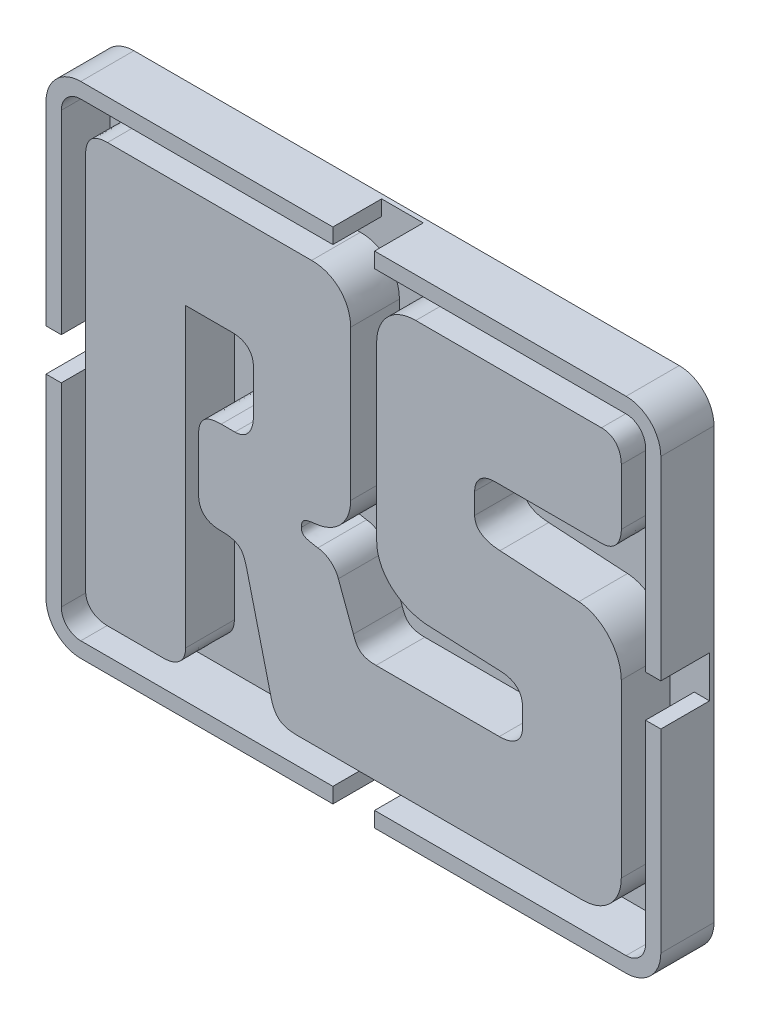
SolidWorks part; units mm, degrees
ref_plane "Front Plane" through (0, 0, 0) normal (0, 0, 1) x (1, 0, 0)
ref_plane "Top Plane" through (0, 0, 0) normal (0, 1, 0) x (1, 0, 0)
ref_plane "Right Plane" through (0, 0, 0) normal (1, 0, 0) x (0, 0, -1)
sketch "Sketch1" plane through (0, 0, 0) normal (0, 0, 1) x (1, 0, 0)
  line L0 (40.5984, 31.4849) -> (40.5984, 17.9224)
  line L1 (40.5984, 17.9224) -> (41.6324, 17.9224)
  line L2 (41.6324, 17.9224) -> (41.6324, 31.4849)
  line L3 (39.2783, 33.8385) -> (21.8474, 33.8385)
  line L4 (21.8474, 33.8385) -> (21.8474, 32.8044)
  line L5 (21.8474, 32.8044) -> (39.2783, 32.8044)
  line L6 (1.0341, 2.3536) -> (1.0341, 15.9005)
  line L7 (1.0341, 15.9005) -> (0, 15.9005)
  line L8 (0, 15.9005) -> (0, 2.3536)
  line L9 (2.3549, 0) -> (19.8255, 0)
  line L10 (19.8255, 0) -> (19.8255, 1.0341)
  line L11 (19.8255, 1.0341) -> (2.3549, 1.0341)
  line L12 (0, 31.4849) -> (0, 17.9225)
  line L13 (0, 17.9225) -> (1.0341, 17.9225)
  line L14 (1.0341, 17.9225) -> (1.0341, 31.4849)
  line L15 (2.3549, 32.8045) -> (19.8256, 32.8045)
  line L16 (19.8256, 32.8045) -> (19.8256, 33.8385)
  line L17 (19.8256, 33.8385) -> (2.3549, 33.8385)
  line L18 (40.5984, 15.9006) -> (40.5984, 2.3536)
  line L19 (39.2783, 1.0341) -> (21.8474, 1.0341)
  line L20 (21.8474, 1.0341) -> (21.8474, 0.0001)
  line L21 (21.8474, 0.0001) -> (39.2788, 0.0001)
  line L22 (41.6324, 2.3542) -> (41.6324, 15.9006)
  line L23 (41.6324, 15.9006) -> (40.5984, 15.9006)
  line L24 (30.4178, 24.3897) -> (37.612, 24.3844)
  line L25 (37.6119, 31.1578) -> (25.0374, 31.1624)
  line L26 (25.7334, 13.6975) -> (30.7888, 13.4646)
  line L27 (32.2731, 12.0731) -> (32.2718, 10.8666)
  line L28 (30.6966, 9.5909) -> (22.3472, 9.5909)
  line L29 (20.8154, 10.6573) -> (19.7956, 13.3946)
  line L30 (20.6305, 18.4034) -> (20.6305, 28.5623)
  line L31 (17.9866, 31.1605) -> (4.1631, 31.1605)
  line L32 (2.6794, 29.6753) -> (2.6794, 4.1632)
  line L33 (9.4513, 4.1632) -> (9.4513, 24.2491)
  line L34 (9.4513, 24.2491) -> (12.6055, 24.2491)
  line L35 (14.0435, 22.9496) -> (14.0435, 20.0279)
  line L36 (12.7913, 18.4963) -> (11.8629, 18.4963)
  line L37 (10.3333, 17.1511) -> (10.3333, 13.5799)
  line L38 (13.5804, 10.9359) -> (15.25, 4.1175)
  line L39 (17.1054, 2.8175) -> (36.3092, 2.8181)
  line L40 (38.9536, 5.4147) -> (38.9536, 17.0373)
  line L41 (36.0776, 20.1908) -> (30.7423, 20.5153)
  line L42 (29.0263, 21.7218) -> (29.0263, 23.1376)
  spline S0 degree 3 poles (41.6324, 31.4849) (41.6324, 32.7827) (40.5763, 33.8385) (39.2783, 33.8385) knots 0 0 0 0 1 1 1 1
  spline S1 degree 3 poles (39.2783, 32.8044) (40.0061, 32.8044) (40.5984, 32.2125) (40.5984, 31.4849) knots 0 0 0 0 1 1 1 1
  spline S2 degree 3 poles (0, 2.3536) (0, 1.0558) (1.0564, 0) (2.3549, 0) knots 0 0 0 0 1 1 1 1
  spline S3 degree 3 poles (2.3549, 1.0341) (1.6266, 1.0341) (1.0341, 1.626) (1.0341, 2.3536) knots 0 0 0 0 1 1 1 1
  spline S4 degree 3 poles (2.3549, 33.8385) (1.0564, 33.8385) (0, 32.7827) (0, 31.4849) knots 0 0 0 0 1 1 1 1
  spline S5 degree 3 poles (1.0341, 31.4849) (1.0341, 32.2125) (1.6266, 32.8045) (2.3549, 32.8045) knots 0 0 0 0 1 1 1 1
  spline S6 degree 3 poles (40.5984, 2.3536) (40.5984, 1.6261) (40.0061, 1.0341) (39.2783, 1.0341) knots 0 0 0 0 1 1 1 1
  spline S7 degree 3 poles (39.2788, 0.0001) (40.5769, 0.0004) (41.6327, 1.0564) (41.6324, 2.3542) knots 0 0 0 0 1 1 1 1
  spline S8 degree 3 poles (37.612, 24.3844) (38.6319, 24.3844) (38.9565, 25.2192) (38.9565, 25.8695) knots 0 0 0 0 1 1 1 1
  spline S9 degree 3 poles (38.9565, 25.8695) (38.9565, 26.0419) (38.9571, 29.26) (38.9571, 29.6726) knots 0 0 0 0 1 1 1 1
  spline S10 degree 3 poles (38.9571, 29.6726) (38.9571, 30.323) (38.6319, 31.1578) (37.6119, 31.1578) knots 0 0 0 0 1 1 1 1
  spline S11 degree 3 poles (25.0374, 31.1624) (23.367, 31.1624) (22.393, 29.9102) (22.393, 28.5651) knots 0 0 0 0 1 1 1 1
  spline S12 degree 3 poles (22.393, 28.5651) (22.393, 27.875) (22.3936, 17.6103) (22.3936, 16.8974) knots 0 0 0 0 1 1 1 1
  spline S13 degree 3 poles (22.3936, 16.8974) (22.3936, 15.1813) (23.878, 13.882) (25.7334, 13.6975) knots 0 0 0 0 1 1 1 1
  spline S14 degree 3 poles (30.7888, 13.4646) (31.9028, 13.4188) (32.2731, 12.8156) (32.2731, 12.0731) knots 0 0 0 0 1 1 1 1
  spline S15 degree 3 poles (32.2718, 10.8666) (32.2423, 10.073) (31.6889, 9.5909) (30.6966, 9.5909) knots 0 0 0 0 1 1 1 1
  spline S16 degree 3 poles (22.3472, 9.5909) (21.1878, 9.5909) (21.002, 10.1468) (20.8154, 10.6573) knots 0 0 0 0 1 1 1 1
  spline S17 degree 3 poles (19.7956, 13.3946) (19.6104, 13.9507) (19.0537, 14.4618) (18.404, 14.5075) knots 0 0 0 0 1 1 1 1
  spline S18 degree 3 poles (18.404, 14.5075) (17.5235, 14.6461) (17.2912, 14.7389) (17.2912, 15.1563) knots 0 0 0 0 1 1 1 1
  spline S19 degree 3 poles (17.2912, 15.1563) (17.2912, 15.7139) (17.5692, 15.7604) (18.3111, 15.8524) knots 0 0 0 0 1 1 1 1
  spline S20 degree 3 poles (18.3111, 15.8524) (19.6104, 15.9919) (20.6305, 17.0119) (20.6305, 18.4034) knots 0 0 0 0 1 1 1 1
  spline S21 degree 3 poles (20.6305, 28.5623) (20.6305, 29.9081) (19.6568, 31.1605) (17.9866, 31.1605) knots 0 0 0 0 1 1 1 1
  spline S22 degree 3 poles (4.1631, 31.1605) (3.1426, 31.1605) (2.6794, 30.6501) (2.6794, 29.6753) knots 0 0 0 0 1 1 1 1
  spline S23 degree 3 poles (2.6794, 4.1632) (2.6794, 3.1427) (3.5135, 2.8181) (4.1631, 2.8181) knots 0 0 0 0 1 1 1 1
  spline S24 degree 3 poles (4.1631, 2.8181) (4.3355, 2.8181) (7.5542, 2.8175) (7.9669, 2.8175) knots 0 0 0 0 1 1 1 1
  spline S25 degree 3 poles (7.9669, 2.8175) (8.6167, 2.8175) (9.4513, 3.1427) (9.4513, 4.1632) knots 0 0 0 0 1 1 1 1
  spline S26 degree 3 poles (12.6055, 24.2491) (13.4874, 24.2491) (14.0435, 23.7853) (14.0435, 22.9496) knots 0 0 0 0 1 1 1 1
  spline S27 degree 3 poles (14.0435, 20.0279) (14.0435, 19.2383) (13.674, 18.4963) (12.7913, 18.4963) knots 0 0 0 0 1 1 1 1
  spline S28 degree 3 poles (11.8629, 18.4963) (10.7971, 18.4963) (10.3333, 18.0788) (10.3333, 17.1511) knots 0 0 0 0 1 1 1 1
  spline S29 degree 3 poles (10.3333, 13.5799) (10.3333, 12.6521) (10.9358, 12.2345) (11.7706, 12.2345) knots 0 0 0 0 1 1 1 1
  spline S30 degree 3 poles (11.7706, 12.2345) (13.1623, 12.2345) (13.3487, 11.7707) (13.5804, 10.9359) knots 0 0 0 0 1 1 1 1
  spline S31 degree 3 poles (15.25, 4.1175) (15.5286, 3.0033) (16.1311, 2.8175) (17.1054, 2.8175) knots 0 0 0 0 1 1 1 1
  spline S32 degree 3 poles (36.3092, 2.8181) (37.9795, 2.8181) (38.9536, 4.0711) (38.9536, 5.4147) knots 0 0 0 0 1 1 1 1
  spline S33 degree 3 poles (38.9536, 17.0373) (38.9536, 18.5677) (37.7014, 20.0979) (36.0776, 20.1908) knots 0 0 0 0 1 1 1 1
  spline S34 degree 3 poles (30.7423, 20.5153) (29.6294, 20.5617) (29.0263, 21.0256) (29.0263, 21.7218) knots 0 0 0 0 1 1 1 1
  spline S35 degree 3 poles (29.0263, 23.1376) (29.0263, 23.7871) (29.4444, 24.3897) (30.4178, 24.3897) knots 0 0 0 0 1 1 1 1
sketch "Sketch2" plane through (0, 0, 0) normal (0, 0, 1) x (1, 0, 0)
  line L2 (2.3536, 0.0001) -> (39.2788, 0.0001)
  line L3 (0, 2.3537) -> (0, 31.4849)
  line L4 (2.3549, 33.8385) -> (39.2788, 33.8385)
  line L6 (41.6324, 2.3537) -> (41.6324, 31.4849)
  arc A0 (39.2788, 33.8385) -> (41.6324, 31.4849) centre (39.2788, 31.4849) cw
  arc A1 (41.6324, 2.3537) -> (39.2788, 0.0001) centre (39.2788, 2.3537) cw
  arc A2 (2.3536, 0.0001) -> (0, 2.3537) centre (2.3536, 2.3537) cw
  arc A3 (0, 31.4849) -> (2.3549, 33.8385) centre (2.3536, 31.4849) cw
extrude "Boss-Extrude1" add sketch "Sketch2" along normal blind 3.6
sketch "Sketch6" plane through (0, 0, 3.6) normal (0, 0, 1) x (1, 0, 0)
  line L0 (40.5984, 31.4849) -> (40.5984, 18.3225)
  line L1 (40.5984, 18.3225) -> (42.9082, 18.3225)
  line L2 (-0.414, 18.3225) -> (-0.414, 15.5005)
  line L3 (19.4255, 34.3512) -> (22.2474, 34.3512)
  line L4 (22.2474, 34.3512) -> (22.2474, 32.8044)
  line L5 (22.2474, 32.8044) -> (39.2783, 32.8044)
  line L6 (1.0341, 2.3555) -> (1.0341, 15.5005)
  line L7 (1.0341, 15.5005) -> (-0.414, 15.5005)
  line L8 (0, 17.9225) -> (1.0341, 17.9225) construction
  line L9 (42.9082, 15.5005) -> (42.9082, 18.3225)
  line L10 (19.4255, -1.1352) -> (19.4255, 1.036)
  line L11 (19.4255, 1.036) -> (2.3549, 1.036)
  line L12 (22.2474, -1.1352) -> (19.4255, -1.1352)
  line L13 (-0.414, 18.3225) -> (1.0341, 18.3225)
  line L14 (1.0341, 18.3225) -> (1.0341, 31.4849)
  line L15 (2.3549, 32.8045) -> (19.4255, 32.8045)
  line L16 (19.4255, 32.8045) -> (19.4255, 34.3512)
  line L17 (1.0341, 15.9005) -> (0, 15.9005) construction
  line L18 (40.5984, 15.5005) -> (40.5984, 2.3555)
  line L19 (39.2783, 1.036) -> (22.2474, 1.036)
  line L20 (22.2474, 1.036) -> (22.2474, -1.1352)
  line L21 (19.8255, 0) -> (19.8255, 1.0341) construction
  line L22 (21.8474, 1.0341) -> (21.8474, 0.0001) construction
  line L23 (42.9082, 15.5005) -> (40.5984, 15.5005)
  line L24 (30.4178, 24.3897) -> (37.612, 24.3844)
  line L25 (37.6119, 31.1578) -> (25.0374, 31.1624)
  line L26 (25.7334, 13.6975) -> (30.7888, 13.4646)
  line L27 (32.2731, 12.0731) -> (32.2718, 10.8666)
  line L28 (30.6966, 9.5909) -> (22.3472, 9.5909)
  line L29 (20.8154, 10.6573) -> (19.7956, 13.3946)
  line L30 (20.6305, 18.4034) -> (20.6305, 28.5623)
  line L31 (17.9866, 31.1605) -> (4.1631, 31.1605)
  line L32 (2.6794, 29.6753) -> (2.6794, 4.1632)
  line L33 (9.4513, 4.1632) -> (9.4513, 24.2491)
  line L34 (9.4513, 24.2491) -> (12.6055, 24.2491)
  line L35 (14.0435, 22.9496) -> (14.0435, 20.0279)
  line L36 (12.7913, 18.4963) -> (11.8629, 18.4963)
  line L37 (10.3333, 17.1511) -> (10.3333, 13.5799)
  line L38 (13.5804, 10.9359) -> (15.25, 4.1175)
  line L39 (17.1054, 2.8175) -> (36.3092, 2.8181)
  line L40 (38.9536, 5.4147) -> (38.9536, 17.0373)
  line L41 (36.0776, 20.1908) -> (30.7423, 20.5153)
  line L42 (29.0263, 21.7218) -> (29.0263, 23.1376)
  line L43 (40.5984, 15.9006) -> (40.5984, 2.3536) construction
  line L44 (2.3549, 32.8045) -> (19.8256, 32.8045) construction
  spline S1 degree 3 poles (39.2783, 32.8044) (40.0061, 32.8044) (40.5984, 32.2125) (40.5984, 31.4849) knots 0 0 0 0 1 1 1 1
  spline S3 degree 3 poles (2.3549, 1.036) (1.6266, 1.036) (1.0341, 1.6279) (1.0341, 2.3555) knots 0 0 0 0 1 1 1 1
  spline S5 degree 3 poles (1.0341, 31.4849) (1.0341, 32.2125) (1.6266, 32.8045) (2.3549, 32.8045) knots 0 0 0 0 1 1 1 1
  spline S6 degree 3 poles (40.5984, 2.3555) (40.5984, 1.6279) (40.0061, 1.036) (39.2783, 1.036) knots 0 0 0 0 1 1 1 1
  spline S8 degree 3 poles (37.612, 24.3844) (38.6319, 24.3844) (38.9565, 25.2192) (38.9565, 25.8695) knots 0 0 0 0 1 1 1 1
  spline S9 degree 3 poles (38.9565, 25.8695) (38.9565, 26.0419) (38.9571, 29.26) (38.9571, 29.6726) knots 0 0 0 0 1 1 1 1
  spline S10 degree 3 poles (38.9571, 29.6726) (38.9571, 30.323) (38.6319, 31.1578) (37.6119, 31.1578) knots 0 0 0 0 1 1 1 1
  spline S11 degree 3 poles (25.0374, 31.1624) (23.367, 31.1624) (22.393, 29.9102) (22.393, 28.5651) knots 0 0 0 0 1 1 1 1
  spline S12 degree 3 poles (22.393, 28.5651) (22.393, 27.875) (22.3936, 17.6103) (22.3936, 16.8974) knots 0 0 0 0 1 1 1 1
  spline S13 degree 3 poles (22.3936, 16.8974) (22.3936, 15.1813) (23.878, 13.882) (25.7334, 13.6975) knots 0 0 0 0 1 1 1 1
  spline S14 degree 3 poles (30.7888, 13.4646) (31.9028, 13.4188) (32.2731, 12.8156) (32.2731, 12.0731) knots 0 0 0 0 1 1 1 1
  spline S15 degree 3 poles (32.2718, 10.8666) (32.2423, 10.073) (31.6889, 9.5909) (30.6966, 9.5909) knots 0 0 0 0 1 1 1 1
  spline S16 degree 3 poles (22.3472, 9.5909) (21.1878, 9.5909) (21.002, 10.1468) (20.8154, 10.6573) knots 0 0 0 0 1 1 1 1
  spline S17 degree 3 poles (19.7956, 13.3946) (19.6104, 13.9507) (19.0537, 14.4618) (18.404, 14.5075) knots 0 0 0 0 1 1 1 1
  spline S18 degree 3 poles (18.404, 14.5075) (17.5235, 14.6461) (17.2912, 14.7389) (17.2912, 15.1563) knots 0 0 0 0 1 1 1 1
  spline S19 degree 3 poles (17.2912, 15.1563) (17.2912, 15.7139) (17.5692, 15.7604) (18.3111, 15.8524) knots 0 0 0 0 1 1 1 1
  spline S20 degree 3 poles (18.3111, 15.8524) (19.6104, 15.9919) (20.6305, 17.0119) (20.6305, 18.4034) knots 0 0 0 0 1 1 1 1
  spline S21 degree 3 poles (20.6305, 28.5623) (20.6305, 29.9081) (19.6568, 31.1605) (17.9866, 31.1605) knots 0 0 0 0 1 1 1 1
  spline S22 degree 3 poles (4.1631, 31.1605) (3.1426, 31.1605) (2.6794, 30.6501) (2.6794, 29.6753) knots 0 0 0 0 1 1 1 1
  spline S23 degree 3 poles (2.6794, 4.1632) (2.6794, 3.1427) (3.5135, 2.8181) (4.1631, 2.8181) knots 0 0 0 0 1 1 1 1
  spline S24 degree 3 poles (4.1631, 2.8181) (4.3355, 2.8181) (7.5542, 2.8175) (7.9669, 2.8175) knots 0 0 0 0 1 1 1 1
  spline S25 degree 3 poles (7.9669, 2.8175) (8.6167, 2.8175) (9.4513, 3.1427) (9.4513, 4.1632) knots 0 0 0 0 1 1 1 1
  spline S26 degree 3 poles (12.6055, 24.2491) (13.4874, 24.2491) (14.0435, 23.7853) (14.0435, 22.9496) knots 0 0 0 0 1 1 1 1
  spline S27 degree 3 poles (14.0435, 20.0279) (14.0435, 19.2383) (13.674, 18.4963) (12.7913, 18.4963) knots 0 0 0 0 1 1 1 1
  spline S28 degree 3 poles (11.8629, 18.4963) (10.7971, 18.4963) (10.3333, 18.0788) (10.3333, 17.1511) knots 0 0 0 0 1 1 1 1
  spline S29 degree 3 poles (10.3333, 13.5799) (10.3333, 12.6521) (10.9358, 12.2345) (11.7706, 12.2345) knots 0 0 0 0 1 1 1 1
  spline S30 degree 3 poles (11.7706, 12.2345) (13.1623, 12.2345) (13.3487, 11.7707) (13.5804, 10.9359) knots 0 0 0 0 1 1 1 1
  spline S31 degree 3 poles (15.25, 4.1175) (15.5286, 3.0033) (16.1311, 2.8175) (17.1054, 2.8175) knots 0 0 0 0 1 1 1 1
  spline S32 degree 3 poles (36.3092, 2.8181) (37.9795, 2.8181) (38.9536, 4.0711) (38.9536, 5.4147) knots 0 0 0 0 1 1 1 1
  spline S33 degree 3 poles (38.9536, 17.0373) (38.9536, 18.5677) (37.7014, 20.0979) (36.0776, 20.1908) knots 0 0 0 0 1 1 1 1
  spline S34 degree 3 poles (30.7423, 20.5153) (29.6294, 20.5617) (29.0263, 21.0256) (29.0263, 21.7218) knots 0 0 0 0 1 1 1 1
  spline S35 degree 3 poles (29.0263, 23.1376) (29.0263, 23.7871) (29.4444, 24.3897) (30.4178, 24.3897) knots 0 0 0 0 1 1 1 1
  dimension "D1" = 0.4
  dimension "D2" = 0.4
  dimension "D3" = 0.4
  dimension "D4" = 0.4
extrude "Cut-Extrude1" cut sketch "Sketch6" against normal offset from surface (3.3 mm away) 0.3 up to face at (20.8164, 16.9193, 0)
